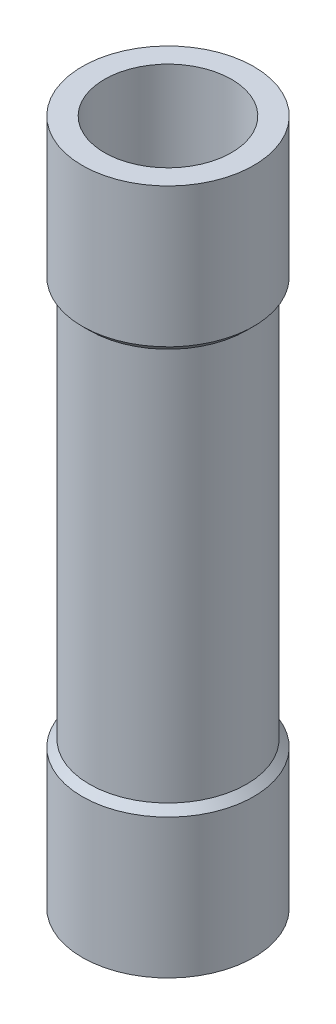
SolidWorks part; units mm, degrees
ref_plane "Front Plane" through (0, 0, 0) normal (0, 0, 1) x (1, 0, 0)
ref_plane "Top Plane" through (0, 0, 0) normal (0, 1, 0) x (1, 0, 0)
ref_plane "Right Plane" through (0, 0, 0) normal (1, 0, 0) x (0, 0, -1)
sketch "Sketch1" plane through (0, 0, 0) normal (0, 0, 1) x (1, 0, 0)
  line L0 (0, 0) -> (0, 50000) construction
  line L1 (2.259, 12.192) -> (2.259, -12.192)
  line L2 (1.016, -7.239) -> (2.159, -7.239)
  line L3 (1.016, -7.239) -> (1.016, 7.239)
  line L4 (1.016, 7.239) -> (2.159, 7.239)
  line L5 (2.159, -7.239) -> (2.159, 7.239)
  line L6 (1.016, -7.239) -> (2.159, 7.239) construction
  line L7 (1.016, 7.239) -> (2.159, -7.239) construction
  line L8 (2.259, -12.192) -> (3.048, -12.192)
  line L9 (3.048, -12.192) -> (3.048, -7.239)
  line L10 (3.048, -7.239) -> (2.794, -6.985)
  line L11 (2.794, -6.985) -> (2.794, 6.985)
  line L12 (2.794, 6.985) -> (3.048, 7.239)
  line L13 (3.048, 7.239) -> (3.048, 12.192)
  line L14 (3.048, 12.192) -> (2.259, 12.192)
  line L15 (2.794, 0) -> (0, 0) construction
  point P3 (1.5875, 0)
  dimension "D1" = 2.032
  dimension "D2" = 4.318
  dimension "D3" = 14.478
  dimension "D4" = 0.1
  dimension "D5" = 5.588
  dimension "D6" = 6.096
  dimension "D7" = 24.384
revolve "Revolve1" add sketch "Sketch1" angle 360 about L0
